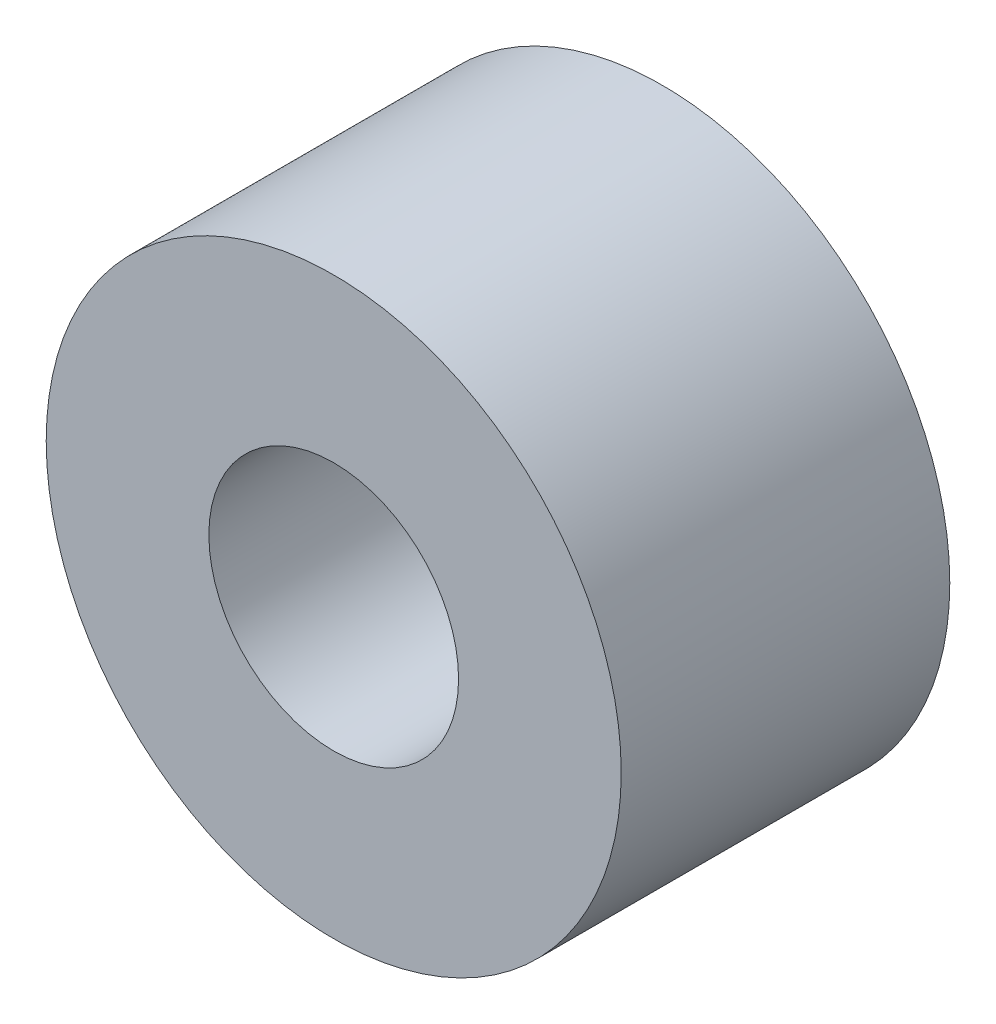
SolidWorks part; units mm, degrees
material "1060 Alloy"
ref_plane "Front Plane" through (0, 0, 0) normal (0, 0, 1) x (1, 0, 0)
ref_plane "Top Plane" through (0, 0, 0) normal (0, 1, 0) x (1, 0, 0)
ref_plane "Right Plane" through (0, 0, 0) normal (1, 0, 0) x (0, 0, -1)
sketch "Sketch1" plane through (0, 0, 0) normal (0, 0, 1) x (1, 0, 0)
  circle A0 centre (0, 0) radius 5.5562
  dimension "D1" = 11.1125
extrude "Boss-Extrude1" add sketch "Sketch1" along normal mid plane 6.35
sketch "Sketch2" plane through (0, 0, 3.175) normal (0, 0, 1) x (1, 0, 0)
  circle A0 centre (0, 0) radius 2.413
  dimension "D1" = 4.826
extrude "Cut-Extrude1" cut sketch "Sketch2" against normal through all
